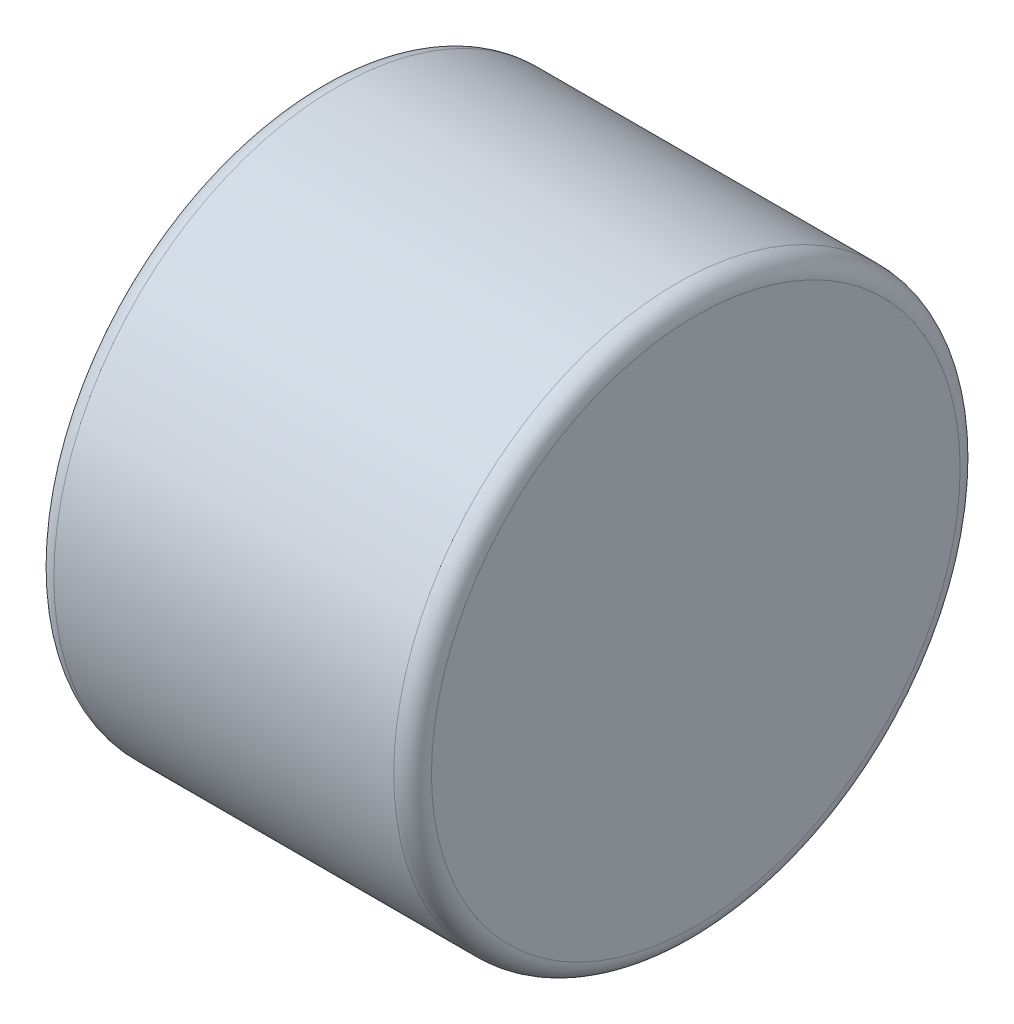
SolidWorks part; units mm, degrees
ref_plane "Front Plane" through (0, 0, 0) normal (0, 0, 1) x (1, 0, 0)
ref_plane "Top Plane" through (0, 0, 0) normal (0, 1, 0) x (1, 0, 0)
ref_plane "Right Plane" through (0, 0, 0) normal (1, 0, 0) x (0, 0, -1)
sketch "Sketch1" plane through (0, 0, 0) normal (1, 0, 0) x (0, 0, -1)
  circle A0 centre (0, 0) radius 3
  dimension "D1" = 6
extrude "Boss-Extrude1" add sketch "Sketch1" along normal mid plane 4
fillet "Fillet1" radius 0.2 2 edges at (2, 0, -3) (-2, 0, -3)
